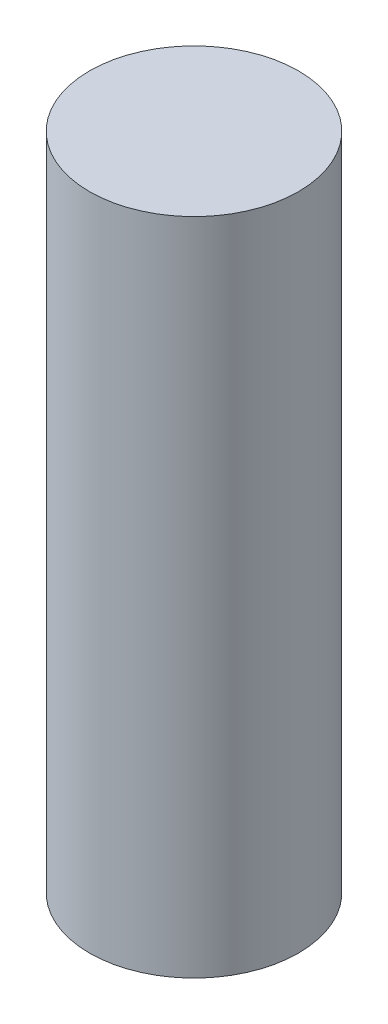
SolidWorks part; units mm, degrees
ref_plane "Front Plane" through (0, 0, 0) normal (0, 0, 1) x (1, 0, 0)
ref_plane "Top Plane" through (0, 0, 0) normal (0, 1, 0) x (1, 0, 0)
ref_plane "Right Plane" through (0, 0, 0) normal (1, 0, 0) x (0, 0, -1)
sketch "Sketch1" plane through (0, 0, 0) normal (0, 1, 0) x (1, 0, 0)
  circle A0 centre (0, 0) radius 6.5
extrude "Extrude1" add sketch "Sketch1" against normal blind 41
